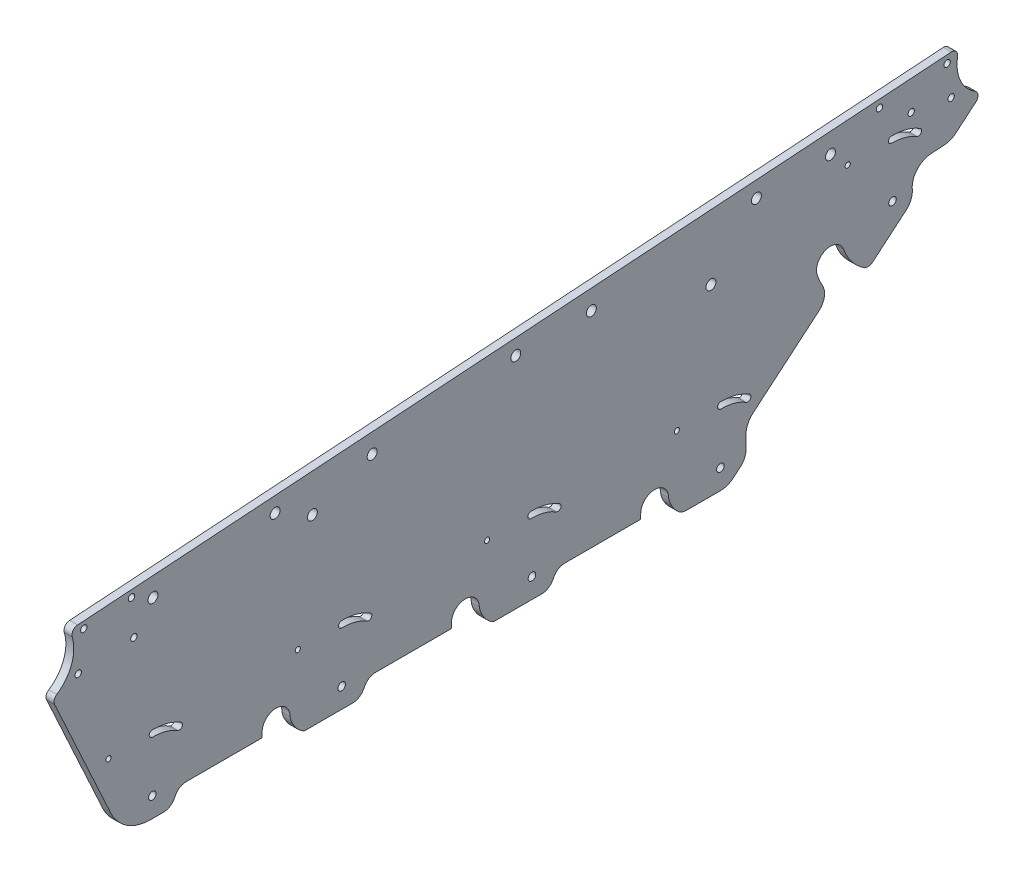
SolidWorks part; units mm, degrees
ref_plane "前视基准面" through (0, 0, 0) normal (0, 0, 1) x (1, 0, 0)
ref_plane "上视基准面" through (0, 0, 0) normal (0, 1, 0) x (1, 0, 0)
ref_plane "右视基准面" through (0, 0, 0) normal (1, 0, 0) x (0, 0, -1)
sketch "草图1" plane through (0, 0, 0) normal (-1, 0, 0) x (0, 0, 1)
  line L0 (79.9418, 312.7793) -> (79.9418, 310.3794)
  line L1 (-15.0582, 312.7793) -> (-15.0582, 310.3548)
  line L2 (-262.4713, 396.8637) -> (-255.6293, 396.4086)
  line L3 (-110.0582, 312.7793) -> (-110.0582, 310.3752)
  line L4 (-162.9047, 314.2174) -> (-162.9047, 320.7531)
  line L5 (-278.2528, 407.6106) -> (-268.2462, 399.1902)
  line L8 (-225.9662, 363.5596) -> (-242.7807, 377.7089)
  line L9 (-199.49, 356.194) -> (-166.4661, 328.4045)
  line L12 (79.9418, 310.3794) -> (118.0488, 310.3794)
  line L13 (-15.0582, 310.3548) -> (23.0756, 310.3548)
  line L14 (-110.0582, 310.3752) -> (-71.8978, 310.3752)
  line L42 (129.3553, 302.7793) -> (135.8467, 302.7793)
  line L53 (34.3713, 302.7793) -> (58.6944, 302.7793)
  line L54 (-60.5308, 302.7793) -> (-36.3056, 302.7793)
  line L62 (-265.9135, 435.515) -> (172.5491, 405.7332)
  line L63 (155.833, 315.5843) -> (184.1003, 377.0265)
  line L65 (-156.5281, 305.1279) -> (-160.0556, 308.0962)
  line L68 (-150.0895, 302.7793) -> (-132.9628, 302.7793)
  circle A0 centre (134.6976, 398.7144) radius 2.5
  circle A1 centre (-205.3024, 421.3291) radius 2.5
  circle A3 centre (24.6976, 406.0309) radius 2.5
  arc A4 (-156.5281, 305.1279) -> (-150.0895, 302.7793) centre (-150.0895, 312.7793) ccw
  arc A5 (135.8467, 302.7793) -> (155.833, 315.5843) centre (135.8467, 324.7793) ccw
  circle A6 centre (54.6976, 394.7144) radius 2.5
  arc A7 (-66.5574, 307.1102) -> (-65.2315, 305.0506) centre (-55.4881, 312.7793) ccw
  circle A8 centre (-145.3024, 394.7144) radius 2.5
  circle A10 centre (-85.3024, 413.3475) radius 2.5
  arc A11 (28.4469, 307.0285) -> (29.4805, 305.3037) centre (40, 312.7793) ccw
  arc A12 (123.4249, 307.0434) -> (124.4598, 305.3102) centre (135, 312.7793) ccw
  arc A13 (123.4249, 307.0434) -> (118.0488, 310.3794) centre (118.0488, 304.3794) ccw
  arc A14 (23.0756, 310.3548) -> (28.4469, 307.0285) centre (23.0756, 304.3548) cw
  arc A15 (-71.8978, 310.3752) -> (-66.5574, 307.1102) centre (-71.8978, 304.3752) cw
  circle A18 centre (-229.9125, 429.2269) radius 1.6
  circle A19 centre (-263.8307, 431.5848) radius 1.6
  circle A21 centre (-245.8276, 419.3316) radius 1.6
  arc A22 (-129.3492, 303.9896) -> (-132.9628, 302.7793) centre (-132.9628, 308.7793) cw
  arc A23 (34.3713, 302.7793) -> (29.4805, 305.3037) centre (34.3713, 308.7793) cw
  circle A24 centre (-213.9248, 412.4193) radius 1.3
  arc A25 (-60.5308, 302.7793) -> (-65.2315, 305.0506) centre (-60.5308, 308.7793) cw
  arc A26 (-205.3024, 374.4129) -> (-218.7886, 357.5197) centre (-236.4128, 385.4193) cw construction
  arc A27 (-199.49, 356.194) -> (-201.3514, 366.1658) centre (-194.3391, 362.3151) cw
  arc A28 (-222.5271, 363.4378) -> (-225.9662, 363.5596) centre (-224.1031, 367.5509) cw
  arc A29 (-222.5271, 363.4378) -> (-211.9016, 376.7476) centre (-236.4128, 385.4193) ccw
  arc A30 (129.3553, 302.7793) -> (124.4598, 305.3102) centre (129.3553, 308.7793) cw
  arc A31 (-166.4661, 328.4045) -> (-162.9047, 320.7531) centre (-172.9047, 320.7531) cw
  arc A32 (-262.4713, 396.8637) -> (-268.2462, 399.1902) centre (-261.8076, 406.8416) cw
  arc A33 (-255.6293, 396.4086) -> (-246.3447, 385.4148) centre (-256.293, 386.4306) cw
  arc A34 (-246.3447, 385.4148) -> (-242.7807, 377.7089) centre (-237.5156, 384.8212) ccw
  arc A35 (-162.9047, 314.2174) -> (-160.0556, 308.0962) centre (-154.9047, 314.2174) ccw
  arc A36 (-198.7032, 372.0782) -> (-211.9016, 376.7476) centre (-205.3024, 374.4129) ccw
  arc A37 (-201.3514, 366.1658) -> (-198.7032, 372.0782) centre (-236.4128, 385.4193) ccw
  arc A38 (184.1003, 377.0265) -> (182.9947, 380.8056) centre (181.3749, 378.2804) ccw
  arc A39 (172.5491, 405.7332) -> (175.2178, 401.873) centre (172.3458, 402.7401) cw
  arc A40 (-278.2528, 407.6106) -> (-277.8828, 412.4676) centre (-276.3212, 409.9061) cw
  arc A41 (-265.9135, 435.515) -> (-269.0706, 431.9978) centre (-266.1168, 432.5219) ccw
  arc A42 (-235.9248, 412.4193) -> (-249.4461, 408.7897) centre (-236.4128, 387.2375) ccw construction
  arc A43 (-235.8937, 414.019) -> (-250.274, 410.1588) centre (-236.4128, 387.2375) ccw
  arc A44 (-235.9558, 410.8196) -> (-248.6181, 407.4205) centre (-236.4128, 387.2375) ccw
  arc A45 (-235.9558, 410.8196) -> (-235.8937, 414.019) centre (-235.9248, 412.4193) ccw
  arc A46 (-250.274, 410.1588) -> (-248.6181, 407.4205) centre (-249.4461, 408.7897) ccw
  circle A47 centre (-265.8276, 415.7099) radius 1.6
  circle A48 centre (145.4523, 404.1659) radius 1.6
  circle A50 centre (172.2236, 384.3846) radius 1.6
  circle A51 centre (169.3971, 402.5395) radius 1.6
  circle A52 centre (144.2828, 386.2039) radius 1.6
  circle A132 centre (-236.4128, 385.4193) radius 1.9
  circle A133 centre (-128.2113, 339.7793) radius 1.3
  arc A138 (-125.8547, 308.0793) -> (-129.3492, 303.9896) centre (-136.8604, 313.9454) cw
  circle A140 centre (62, 339.7793) radius 1.3
  circle A144 centre (40, 312.7793) radius 1.9
  arc A150 (64.1453, 308.0793) -> (65.9418, 312.7793) centre (54.0836, 314.6186) ccw
  circle A156 centre (-47.3651, 412.8285) radius 2.5
  arc A157 (-110.0582, 312.7793) -> (-124.0582, 312.7793) centre (-117.0582, 312.7793) ccw
  arc A162 (-30.8547, 308.0793) -> (-29.0582, 312.7793) centre (-40.9164, 314.6186) ccw
  circle A173 centre (-55.4881, 312.7793) radius 1.9
  circle A174 centre (-33, 339.7793) radius 1.3
  arc A179 (-30.8547, 308.0793) -> (-36.3056, 302.7793) centre (-41.8604, 313.9454) cw
  circle A185 centre (-168.1302, 420.8611) radius 2.5
  circle A186 centre (73.3999, 404.796) radius 2.5
  arc A191 (64.1453, 308.0793) -> (58.6944, 302.7793) centre (53.1396, 313.9454) cw
  arc A196 (79.9418, 312.7793) -> (65.9418, 312.7793) centre (72.9418, 312.7793) ccw
  arc A197 (-125.8547, 308.0793) -> (-124.0582, 312.7793) centre (-135.9164, 314.6186) ccw
  circle A198 centre (157, 339.7793) radius 1.3
  arc A201 (-117.0582, 312.7793) -> (-121.1229, 302.7793) centre (-135.9164, 314.6186) cw construction
  circle A202 centre (-150.0582, 312.7793) radius 1.9
  arc A208 (-277.8828, 412.4676) -> (-269.0706, 431.9978) centre (-287.7673, 428.6807) ccw
  circle A214 centre (135, 312.7793) radius 1.9
  arc A220 (175.2178, 401.873) -> (182.9947, 380.8056) centre (193.0538, 396.4879) ccw
  arc A221 (-15.0582, 312.7793) -> (-29.0582, 312.7793) centre (-22.0582, 312.7793) ccw
  arc A226 (-55, 339.7793) -> (-68.5213, 336.1497) centre (-55.4881, 314.5975) ccw construction
  arc A227 (-54.969, 341.379) -> (-69.3493, 337.5188) centre (-55.4881, 314.5975) ccw
  arc A228 (-55.031, 338.1796) -> (-67.6934, 334.7805) centre (-55.4881, 314.5975) ccw
  arc A229 (-55.031, 338.1796) -> (-54.969, 341.379) centre (-55, 339.7793) ccw
  arc A230 (-69.3493, 337.5188) -> (-67.6934, 334.7805) centre (-68.5213, 336.1497) ccw
  arc A231 (-150.2113, 339.7793) -> (-163.7326, 336.1497) centre (-150.6994, 314.5975) ccw construction
  arc A232 (-150.1803, 341.379) -> (-164.5606, 337.5188) centre (-150.6994, 314.5975) ccw
  arc A233 (-150.2423, 338.1796) -> (-162.9047, 334.7805) centre (-150.6994, 314.5975) ccw
  arc A234 (-150.2423, 338.1796) -> (-150.1803, 341.379) centre (-150.2113, 339.7793) ccw
  arc A235 (-164.5606, 337.5188) -> (-162.9047, 334.7805) centre (-163.7326, 336.1497) ccw
  arc A241 (40, 339.7793) -> (26.4787, 336.1497) centre (39.5119, 314.5975) ccw construction
  arc A242 (40.031, 341.379) -> (25.6507, 337.5188) centre (39.5119, 314.5975) ccw
  arc A243 (39.969, 338.1796) -> (27.3066, 334.7805) centre (39.5119, 314.5975) ccw
  arc A244 (39.969, 338.1796) -> (40.031, 341.379) centre (40, 339.7793) ccw
  arc A245 (25.6507, 337.5188) -> (27.3066, 334.7805) centre (26.4787, 336.1497) ccw
  arc A246 (135, 339.7793) -> (121.4787, 336.1497) centre (134.5119, 314.5975) ccw construction
  arc A247 (135.031, 341.379) -> (120.6507, 337.5188) centre (134.5119, 314.5975) ccw
  arc A248 (134.969, 338.1796) -> (122.3066, 334.7805) centre (134.5119, 314.5975) ccw
  arc A249 (134.969, 338.1796) -> (135.031, 341.379) centre (135, 339.7793) ccw
  arc A250 (120.6507, 337.5188) -> (122.3066, 334.7805) centre (121.4787, 336.1497) ccw
  point P0 (-150, 0)
  point P1 (135, 0)
  point P9 (-344.9533, 138.7825)
  point P10 (187.1329, 101.1747)
  point P11 (165.9429, -19)
  point P12 (-156.9154, -19)
  point P67 (-210.6231, 364.8307)
  point P72 (-211.6166, 365.2818)
  point P90 (-265.7372, 397.0266)
  point P108 (-242.9427, 411.5628)
  point P288 (-31.725, 307.5809)
  point P313 (68.6487, 307.479)
  point P318 (-131.7259, 307.5821)
  point P340 (-62.0179, 338.9228)
  point P357 (-157.2292, 338.9228)
  point P380 (32.9821, 338.9228)
  point P392 (127.9821, 338.9228)
  dimension "D7" = 10
  dimension "D8" = 8
  dimension "D9" = 7
  dimension "D10" = 10
  dimension "D4" = 6
  dimension "D11" = 10
  dimension "D12" = 10
  dimension "D13" = 10
  dimension "D14" = 24
  dimension "D15" = 27
  dimension "D16" = 10
  dimension "D17" = 27
  dimension "D18" = 27
  dimension "D19" = 27
  dimension "D20" = 8
  dimension "D6" = 6
  dimension "D5" = 6
  dimension "D21" = 10
  dimension "D22" = 3
  dimension "D23" = 18
  dimension "D24" = 3.2
  dimension "D25" = 16
  dimension "D28" = 3.78
  dimension "D29" = 34
  dimension "D30" = 28
  dimension "D31" = 3.2
  dimension "D32" = 3.2
  dimension "D33" = 3.2
  dimension "D35" = 20
  dimension "D36" = 3.834
  dimension "D39" = 1.6
  dimension "D34" = 3.2
  dimension "D43" = 5
  dimension "D41" = 2.6
  dimension "D40" = 5
  dimension "D44" = 5
  dimension "D2" = 22
  dimension "D1" = 10
  dimension "D3" = 7
  dimension "D26" = 3.8
  dimension "D27" = 9.8953
  dimension "D37" = 3.4
  dimension "D38" = 3.4
extrude "凸台-拉伸1" add sketch "草图1" along normal blind 4
